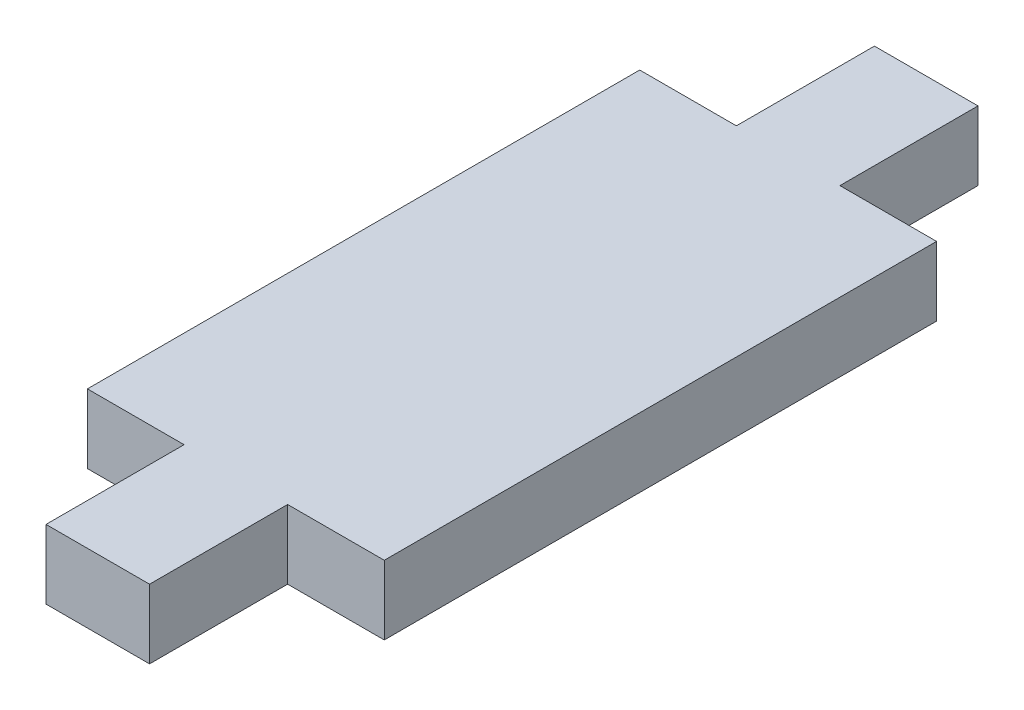
SolidWorks part; units mm, degrees
ref_plane "Front Plane" through (0, 0, 0) normal (0, 0, 1) x (1, 0, 0)
ref_plane "Top Plane" through (0, 0, 0) normal (0, 1, 0) x (1, 0, 0)
ref_plane "Right Plane" through (0, 0, 0) normal (1, 0, 0) x (0, 0, -1)
sketch "Sketch1" plane through (0, 0, 0) normal (0, 1, 0) x (1, 0, 0)
  line L0 (-10.75, 0) -> (10.75, 0) construction
  line L1 (-10.75, 20) -> (-3.75, 20)
  line L2 (-10.75, 20) -> (-10.75, -20)
  line L3 (-10.75, -20) -> (-3.75, -20)
  line L4 (10.75, 20) -> (10.75, -20)
  line L5 (-10.75, 20) -> (10.75, -20) construction
  line L6 (-10.75, -20) -> (10.75, 20) construction
  line L7 (-3.75, -30) -> (3.75, -30)
  line L8 (-3.75, -30) -> (-3.75, -20)
  line L9 (-3.75, -20) -> (3.75, -20) construction
  line L10 (3.75, -30) -> (3.75, -20)
  line L11 (-3.75, -30) -> (3.75, -20) construction
  line L12 (-3.75, -20) -> (3.75, -30) construction
  line L15 (-3.75, 20) -> (3.75, 20) construction
  line L16 (3.75, 30) -> (3.75, 20)
  line L17 (-3.75, 30) -> (3.75, 30)
  line L18 (-3.75, 30) -> (-3.75, 20)
  line L19 (-3.75, 20) -> (3.75, 20) construction
  line L20 (3.75, 20) -> (10.75, 20)
  line L21 (-3.75, -20) -> (3.75, -20) construction
  line L22 (3.75, -20) -> (10.75, -20)
  point P0 (0, 0)
  point P6 (0, -25)
  point P14 (0, 0)
  point P15 (0, 0)
  dimension "D1" = 40
  dimension "D2" = 21.5
  dimension "D3" = 10
  dimension "D4" = 7.5
extrude "Boss-Extrude1" add sketch "Sketch1" along normal blind 5
